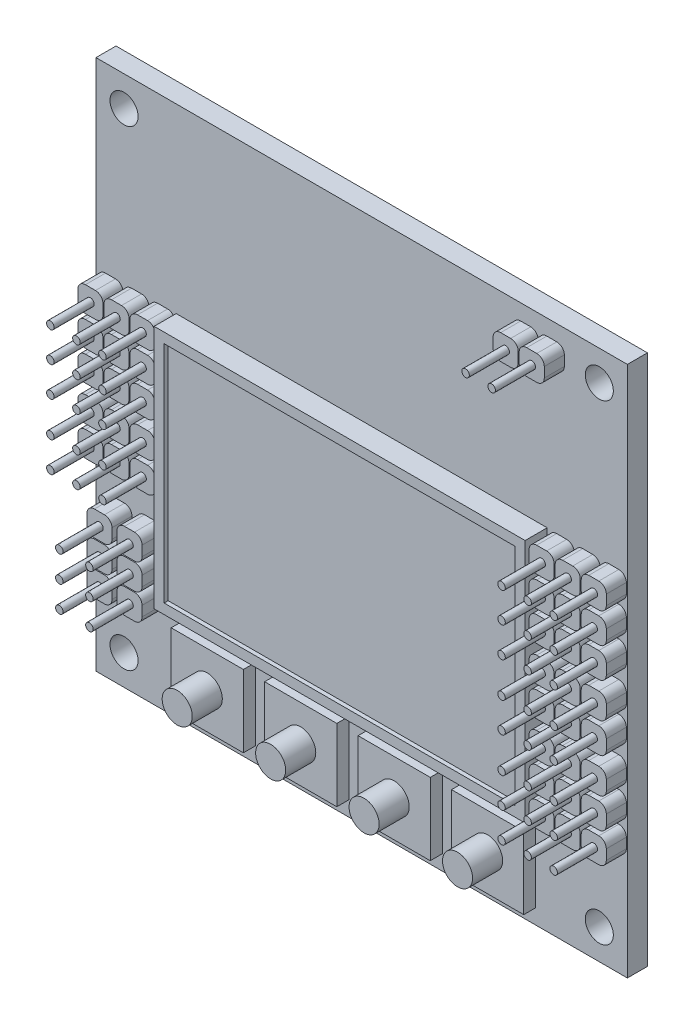
SolidWorks part; units mm, degrees
ref_plane "Front Plane" through (0, 0, 0) normal (0, 0, 1) x (1, 0, 0)
ref_plane "Top Plane" through (0, 0, 0) normal (0, 1, 0) x (1, 0, 0)
ref_plane "Right Plane" through (0, 0, 0) normal (1, 0, 0) x (0, 0, -1)
sketch "Sketch1" plane through (0, 0, 0) normal (0, 0, 1) x (1, 0, 0)
  line L1 (0, 0) -> (53, 0)
  line L2 (0, 0) -> (0, 53)
  line L3 (0, 53) -> (53, 53)
  line L4 (53, 0) -> (53, 53)
  dimension "D1" = 53
  dimension "D2" = 53
extrude "Boss-Extrude1" add sketch "Sketch1" along normal blind 2
sketch "Sketch2" plane through (0, 0, 2) normal (0, 0, 1) x (1, 0, 0)
  line L0 (26.5, 53) -> (26.5, 0) construction
  line L1 (53, 53) -> (0, 53) construction
  line L2 (0, 0) -> (53, 0) construction
  line L3 (0, 26.5) -> (53, 26.5) construction
  line L4 (0, 53) -> (0, 0) construction
  line L5 (53, 0) -> (53, 53) construction
  circle A0 centre (50.2, 50) radius 1.4
  circle A1 centre (2.8, 50) radius 1.4
  circle A2 centre (50.2, 3) radius 1.4
  circle A3 centre (2.8, 3) radius 1.4
  dimension "D3" = 2.8
  dimension "D1" = 3
  dimension "D2" = 2.8
extrude "Cut-Extrude1" cut sketch "Sketch2" against normal up to surface (2 mm away) up to face at (26.5, 26.5, 0)
sketch "Sketch3" plane through (0, 0, 2) normal (0, 0, 1) x (1, 0, 0)
  line L1 (45.9479, 34.8583) -> (46.9479, 34.8583)
  line L2 (45.1979, 34.1083) -> (45.1979, 33.1083)
  line L3 (45.9479, 32.3583) -> (46.9479, 32.3583)
  line L4 (47.6979, 34.1083) -> (47.6979, 33.1083)
  arc A0 (46.9479, 32.3583) -> (47.6979, 33.1083) centre (46.9479, 33.1083) ccw
  arc A1 (45.1979, 33.1083) -> (45.9479, 32.3583) centre (45.9479, 33.1083) ccw
  arc A2 (45.9479, 34.8583) -> (45.1979, 34.1083) centre (45.9479, 34.1083) ccw
  arc A3 (46.9479, 34.8583) -> (47.6979, 34.1083) centre (46.9479, 34.1083) cw
  point P6 (47.6979, 32.3583)
  point P11 (45.1979, 34.8583)
  point P14 (47.6979, 34.8583)
  dimension "D3" = 0.75
  dimension "D1" = 2.5
  dimension "D2" = 2.5
extrude "Boss-Extrude2" add sketch "Sketch3" along normal blind 2
sketch "Sketch4" plane through (0, 0, 4) normal (0, 0, 1) x (1, 0, 0)
  line L0 (45.1979, 34.1083) -> (45.1979, 33.1083) construction
  line L1 (45.1979, 33.6083) -> (47.6979, 33.6083) construction
  line L2 (47.6979, 33.1083) -> (47.6979, 34.1083) construction
  line L3 (46.4479, 34.8583) -> (46.4479, 32.3583) construction
  line L4 (46.9479, 34.8583) -> (45.9479, 34.8583) construction
  line L5 (45.9479, 32.3583) -> (46.9479, 32.3583) construction
  circle A0 centre (46.4479, 33.6083) radius 0.375
  dimension "D1" = 0.75
extrude "Boss-Extrude3" add sketch "Sketch4" along normal blind 4
pattern_linear "LPattern1" count 3 spacing 2.6 along (1, 0, 0) of "Boss-Extrude2", "Boss-Extrude3"
pattern_linear "LPattern2" count 3 spacing 3 along (0, -1, 0) of "Boss-Extrude2", "Boss-Extrude3", "LPattern1"
pattern_linear "LPattern3" count 2 spacing 9.5 along (0, -1, 0) of "Boss-Extrude2", "Boss-Extrude3", "LPattern1"
pattern_linear "LPattern4" count 2 spacing 12.5 along (0, -1, 0) of "Boss-Extrude2", "LPattern1", "Boss-Extrude3"
pattern_linear "LPattern5" count 2 spacing 45 along (-1, 0, 0) of "LPattern4", "LPattern3", "LPattern2", "Boss-Extrude2", "Boss-Extrude3", "LPattern1"
pattern_linear "LPattern6" count 2 spacing 16 along (0, -1, 0) of "LPattern2", "Boss-Extrude2", "Boss-Extrude3", "LPattern1"
sketch "Sketch5" plane through (0, 0, 2) normal (0, 0, 1) x (1, 0, 0)
  line L1 (8.7014, 8.7014) -> (15.9014, 8.7014)
  line L2 (8.7014, 8.7014) -> (8.7014, 1.5014)
  line L3 (8.7014, 1.5014) -> (15.9014, 1.5014)
  line L4 (15.9014, 8.7014) -> (15.9014, 1.5014)
  dimension "D1" = 7.2
  dimension "D2" = 7.2
extrude "Boss-Extrude4" add sketch "Sketch5" along normal blind 1.2
sketch "Sketch6" plane through (0, 0, 3.2) normal (0, 0, 1) x (1, 0, 0)
  line L0 (15.9014, 8.7014) -> (8.7014, 8.7014) construction
  line L1 (8.7014, 8.7014) -> (8.7014, 1.5014) construction
  circle A0 centre (12.3014, 5.1014) radius 1.5
  dimension "D1" = 3
  dimension "D2" = 3.6
  dimension "D3" = 3.6
extrude "Boss-Extrude5" add sketch "Sketch6" along normal blind 3
pattern_linear "LPattern7" count 4 spacing 9.32 along (1, 0, 0) of "Boss-Extrude4", "Boss-Extrude5"
sketch "Sketch7" plane through (0, 0, 2) normal (0, 0, 1) x (1, 0, 0)
  line L1 (42.3622, 51.4261) -> (43.3622, 51.4261)
  line L2 (41.6122, 50.6761) -> (41.6122, 49.6761)
  line L3 (42.3622, 48.9261) -> (43.3622, 48.9261)
  line L4 (44.1122, 50.6761) -> (44.1122, 49.6761)
  arc A0 (43.3622, 48.9261) -> (44.1122, 49.6761) centre (43.3622, 49.6761) ccw
  arc A1 (41.6122, 49.6761) -> (42.3622, 48.9261) centre (42.3622, 49.6761) ccw
  arc A2 (43.3622, 51.4261) -> (44.1122, 50.6761) centre (43.3622, 50.6761) cw
  arc A3 (42.3622, 51.4261) -> (41.6122, 50.6761) centre (42.3622, 50.6761) ccw
  point P8 (41.6122, 48.9261)
  point P11 (44.1122, 51.4261)
  point P14 (41.6122, 51.4261)
  dimension "D3" = 0.75
  dimension "D1" = 2.5
  dimension "D2" = 2.5
extrude "Boss-Extrude6" add sketch "Sketch7" along normal blind 2
sketch "Sketch8" plane through (0, 0, 4) normal (0, 0, 1) x (1, 0, 0)
  line L0 (41.6122, 50.1761) -> (44.1122, 50.1761) construction
  line L1 (41.6122, 50.6761) -> (41.6122, 49.6761) construction
  line L2 (44.1122, 49.6761) -> (44.1122, 50.6761) construction
  line L3 (42.8622, 51.4261) -> (42.8622, 48.9261) construction
  line L4 (43.3622, 51.4261) -> (42.3622, 51.4261) construction
  line L5 (42.3622, 48.9261) -> (43.3622, 48.9261) construction
  circle A0 centre (42.8622, 50.1761) radius 0.375
  dimension "D1" = 0.75
extrude "Boss-Extrude7" add sketch "Sketch8" along normal blind 4
pattern_linear "LPattern8" count 2 spacing 2.6 along (1, 0, 0) of "Boss-Extrude7", "Boss-Extrude6"
sketch "Sketch9" plane through (0, 0, 2) normal (0, 0, 1) x (1, 0, 0)
  line L0 (26.5, 53) -> (26.5, 0) construction
  line L1 (8, 34.8878) -> (45, 34.8878)
  line L2 (8, 34.8878) -> (8, 10.4878)
  line L3 (8, 10.4878) -> (45, 10.4878)
  line L4 (45, 34.8878) -> (45, 10.4878)
  line L5 (53, 53) -> (0, 53) construction
  line L6 (0, 0) -> (53, 0) construction
  point P10 (26.5, 34.8878)
  dimension "D1" = 37
  dimension "D2" = 24.4
extrude "Boss-Extrude8" add sketch "Sketch9" along normal blind 2.2
sketch "Sketch11" plane through (0, 0, 4.2) normal (0, 0, 1) x (1, 0, 0)
  line L0 (9, 33.8878) -> (9, 11.4878)
  line L1 (9, 11.4878) -> (44, 11.4878)
  line L2 (44, 11.4878) -> (44, 33.8878)
  line L3 (44, 33.8878) -> (9, 33.8878)
extrude "Cut-Extrude3" cut sketch "Sketch11" against normal blind 0.4
sketch "Sketch12" plane through (0, 0, 2) normal (0, 0, 1) x (1, 0, 0)
  line L1 (1.8457, 15.9352) -> (2.8457, 15.9352)
  line L2 (1.0957, 15.1852) -> (1.0957, 14.1852)
  line L3 (1.8457, 13.4352) -> (2.8457, 13.4352)
  line L4 (3.5957, 15.1852) -> (3.5957, 14.1852)
  arc A0 (2.8457, 13.4352) -> (3.5957, 14.1852) centre (2.8457, 14.1852) ccw
  arc A1 (1.0957, 14.1852) -> (1.8457, 13.4352) centre (1.8457, 14.1852) ccw
  arc A2 (2.8457, 15.9352) -> (3.5957, 15.1852) centre (2.8457, 15.1852) cw
  arc A3 (1.8457, 15.9352) -> (1.0957, 15.1852) centre (1.8457, 15.1852) ccw
  point P8 (1.0957, 13.4352)
  point P11 (3.5957, 15.9352)
  point P14 (1.0957, 15.9352)
  dimension "D3" = 0.75
  dimension "D1" = 2.5
  dimension "D2" = 2.5
extrude "Boss-Extrude9" add sketch "Sketch12" along normal blind 2
sketch "Sketch13" plane through (0, 0, 4) normal (0, 0, 1) x (1, 0, 0)
  circle A0 centre (2.3457, 14.6852) radius 0.375
  dimension "D1" = 0.75
extrude "Boss-Extrude10" add sketch "Sketch13" along normal up to surface (4 mm away) up to face at (1.8229, 21.1083, 8)
pattern_linear "LPattern9" count 3 spacing 2.6 along (0, -1, 0) of "Boss-Extrude9", "Boss-Extrude10"
pattern_linear "LPattern10" count 2 spacing 3 along (1, 0, 0) of "LPattern9", "Boss-Extrude9", "Boss-Extrude10"
